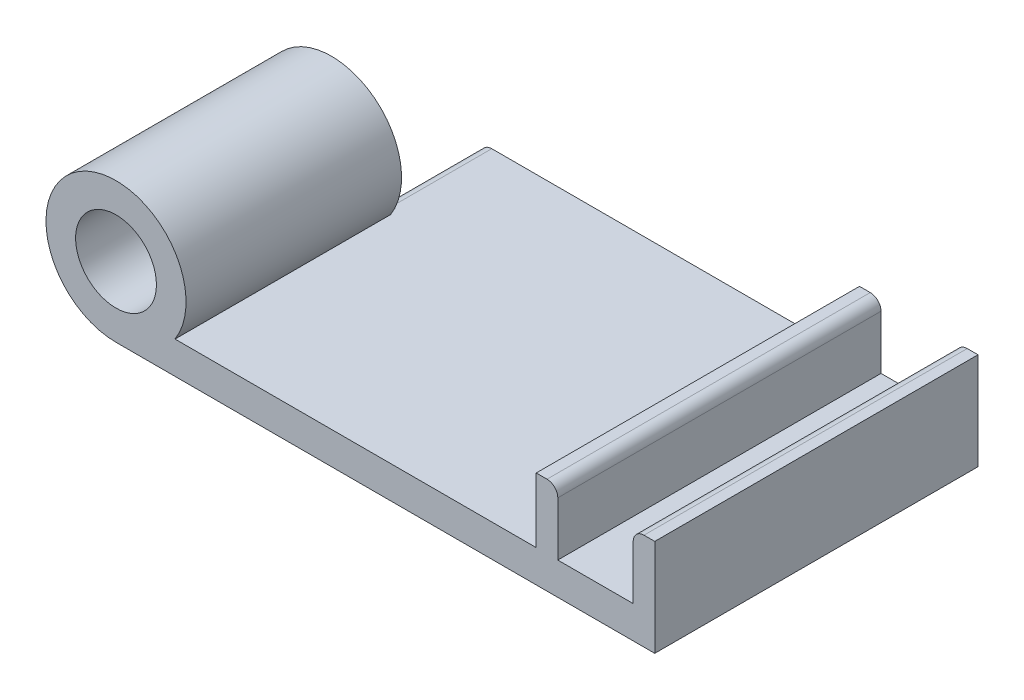
SolidWorks part; units mm, degrees
ref_plane "Front Plane" through (0, 0, 0) normal (0, 0, 1) x (1, 0, 0)
ref_plane "Top Plane" through (0, 0, 0) normal (0, 1, 0) x (1, 0, 0)
ref_plane "Right Plane" through (0, 0, 0) normal (1, 0, 0) x (0, 0, -1)
sketch "Sketch1" plane through (0, 0, 0) normal (0, 0, 1) x (1, 0, 0)
  line L0 (23, 7.5) -> (16, 7.5) construction
  line L1 (-25, -1.5) -> (25, -1.5)
  line L3 (-21.127, 1.5) -> (14, 1.5)
  line L4 (25, -1.5) -> (25, 1.5)
  line L5 (-25, -1.5) -> (25, 1.5) construction
  line L6 (-25, 1.5) -> (25, -1.5) construction
  line L8 (25, 1.5) -> (25, 7.5)
  line L9 (25, 7.5) -> (23, 7.5)
  line L10 (23, 1.5) -> (23, 7.5)
  line L11 (16, 1.5) -> (23, 1.5)
  line L12 (16, 7.5) -> (14, 7.5)
  line L13 (16, 7.5) -> (16, 1.5)
  line L15 (14, 7.5) -> (14, 1.5)
  line L16 (-21.127, 1.5) -> (-25, -1.5)
  arc A1 (-21.127, 1.5) -> (-25, -1.5) centre (-25, 2.5) ccw construction
  circle A2 centre (-25, 2.5) radius 2.1 construction
  point P0 (0, 0)
  dimension "D6" = 4
  dimension "D7" = 4.2
  dimension "D1" = 6
  dimension "D2" = 50
  dimension "D3" = 2
  dimension "D4" = 2
  dimension "D5" = 3
  dimension "D8" = 7
extrude "Boss-Extrude1" add sketch "Sketch1" along normal blind 30
sketch "Sketch3" plane through (0, 0, 30) normal (0, 0, 1) x (1, 0, 0)
  line L0 (-25, -1.5) -> (-25, 5) construction
  circle A0 centre (-25, 5) radius 6.5
  circle A1 centre (-25, 5) radius 3.75
  dimension "6.4" = 7.5
  dimension "D1" = 6.5
extrude "Boss-Extrude2" add sketch "Sketch3" against normal blind 20
sketch "Sketch4" plane through (0, 0, 10) normal (0, 0, -1) x (-1, 0, 0)
  line L1 (21.127, 1.5) -> (25, 1.5)
  line L2 (21.127, 1.5) -> (21.127, -1.5)
  line L3 (21.127, -1.5) -> (25, -1.5)
  line L4 (25, 1.5) -> (25, -1.5)
extrude "Cut-Extrude1" cut sketch "Sketch4" along normal blind 20
fillet "Fillet1" radius 1 3 edges at (-21.127, 1.5, 5) (23, 7.5, 15) (16, 7.5, 15)
